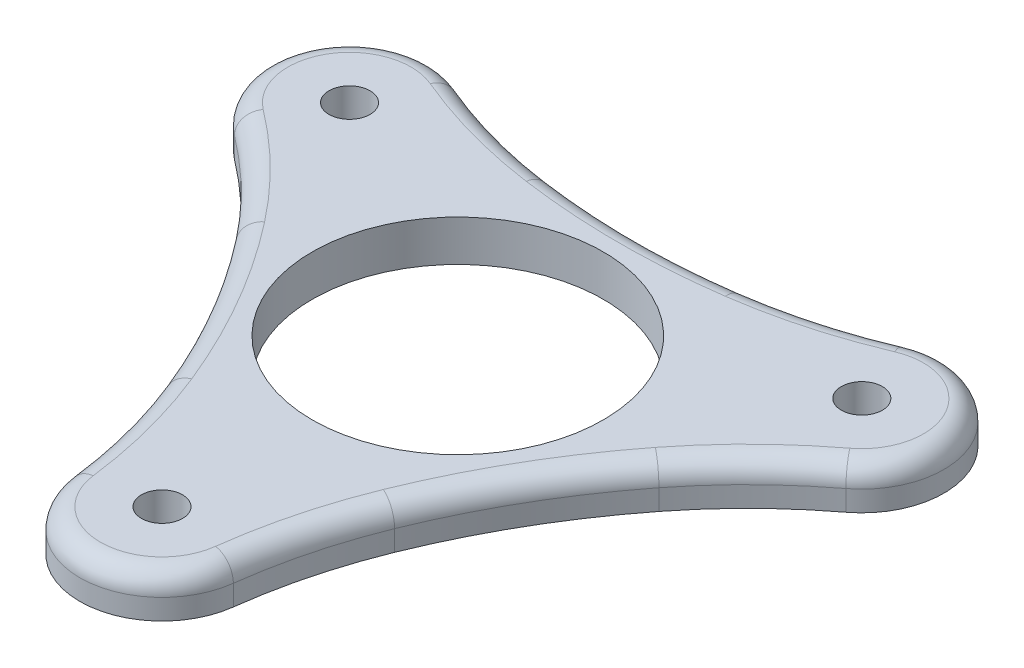
SolidWorks part; units mm, degrees
material "1060 Alloy"
ref_plane "Front Plane" through (0, 0, 0) normal (0, 0, 1) x (1, 0, 0)
ref_plane "Top Plane" through (0, 0, 0) normal (0, 1, 0) x (1, 0, 0)
ref_plane "Right Plane" through (0, 0, 0) normal (1, 0, 0) x (0, 0, -1)
sketch "Sketch1" plane through (0, 0, 0) normal (0, 1, 0) x (1, 0, 0)
  arc A1 (-12.5769, -43.9561) -> (12.5769, -43.9561) centre (0, -45.72) ccw
  arc A2 (-31.7787, 32.87) -> (-44.3556, 11.0861) centre (-39.5947, 22.86) ccw
  arc A3 (44.3556, 11.0861) -> (31.7787, 32.87) centre (39.5947, 22.86) ccw
  circle A4 centre (0, 0) radius 22.5
  circle A5 centre (0, -45.72) radius 3.175
  circle A7 centre (-39.5947, 22.86) radius 3.175
  circle A9 centre (39.5947, 22.86) radius 3.175
  arc A16 (-44.3556, 11.0861) -> (-12.5769, -43.9561) centre (-117.7295, -67.9712) cw
  arc A17 (31.7787, 32.87) -> (-31.7787, 32.87) centre (0, 135.9424) cw
  arc A18 (12.5769, -43.9561) -> (44.3556, 11.0861) centre (117.7295, -67.9712) cw
  point P11 (0, 0)
  point P21 (0, 0)
  point P29 (0, 0)
  dimension "D1" = 25.4
  dimension "D4" = 6.35
  dimension "D5" = 3
  dimension "D7" = 45
  dimension "D6" = 3
  dimension "D3" = 3
extrude "Boss-Extrude4" add sketch "Sketch1" along normal blind 6.35
fillet "Fillet1" radius 78.74 6 edges at (31.7787, 3.175, -32.87) (-31.7787, 3.175, -32.87) (-44.3556, 3.175, -11.0861) (-12.5769, 3.175, 43.9561) (12.5769, 3.175, 43.9561) (44.3556, 3.175, -11.0861)
fillet "Fillet3" radius 3.175 12 edges at (24.32, 6.35, 14.0411) (14.5288, 6.35, 37.2362) (0, 6.35, 58.42) (-14.5288, 6.35, 37.2362) (-24.32, 6.35, 14.0411) (-39.512, 6.35, -6.0358) (-50.5932, 6.35, -29.21) (-24.9831, 6.35, -31.2005) (0, 6.35, -28.0823) (24.9831, 6.35, -31.2005) (50.5932, 6.35, -29.21) (39.512, 6.35, -6.0358)
